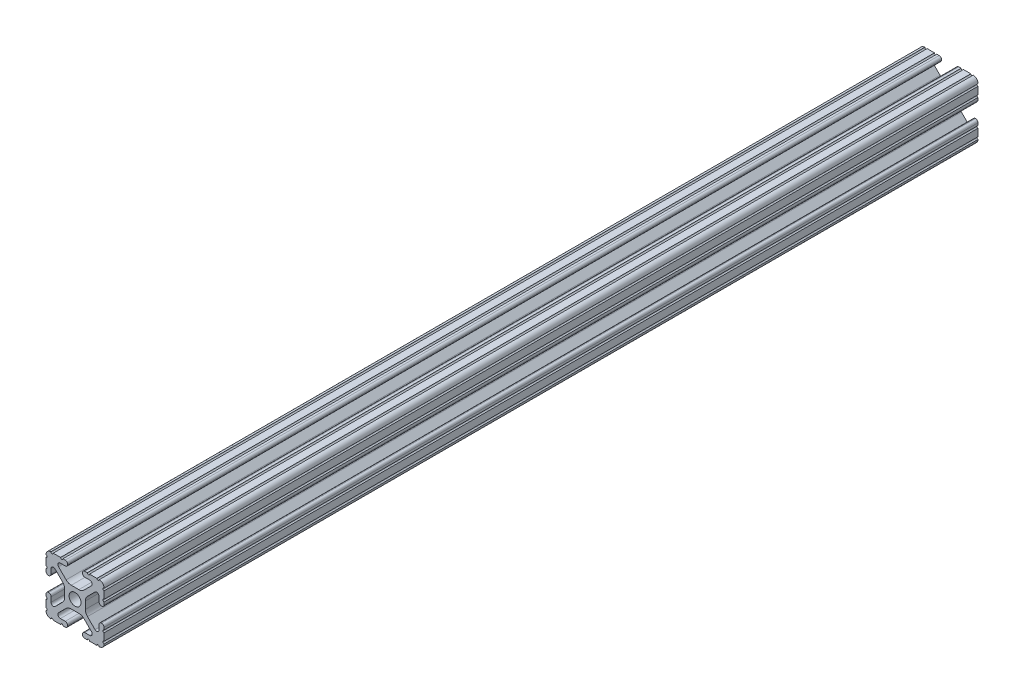
SolidWorks part; units mm, degrees
ref_plane "Front Plane" through (0, 0, 0) normal (0, 0, 1) x (1, 0, 0)
ref_plane "Top Plane" through (0, 0, 0) normal (0, 1, 0) x (1, 0, 0)
ref_plane "Right Plane" through (0, 0, 0) normal (1, 0, 0) x (0, 0, -1)
sketch "Sketch1" plane through (0, 0, 0) normal (0, 0, 1) x (1, 0, 0)
  line L88 (-7.1797, -8.6452) -> (-3.9523, -5.4237)
  line L89 (-1.7093, -4.4958) -> (1.7093, -4.4958)
  line L90 (3.9523, -5.4237) -> (7.1797, -8.6452)
  line L91 (6.4164, -10.4902) -> (4.2875, -10.4902)
  line L92 (3.2385, -11.5392) -> (3.2385, -11.651)
  line L93 (4.2875, -12.7) -> (5.3171, -12.7)
  line L94 (6.3331, -12.7) -> (9.5504, -12.7)
  line L95 (12.7, -9.5504) -> (12.7, -6.3331)
  line L96 (12.7, -5.3171) -> (12.7, -4.2875)
  line L97 (11.651, -3.2385) -> (11.5392, -3.2385)
  line L98 (10.4902, -4.2875) -> (10.4902, -6.4021)
  line L99 (8.7371, -7.1294) -> (5.441, -3.8408)
  line L100 (4.5085, -1.5932) -> (4.5085, 1.5932)
  line L101 (5.441, 3.8408) -> (8.7371, 7.1294)
  line L102 (10.4902, 6.4021) -> (10.4902, 4.2875)
  line L103 (11.5392, 3.2385) -> (11.651, 3.2385)
  line L104 (12.7, 4.2875) -> (12.7, 5.3171)
  line L105 (12.7, 6.3331) -> (12.7, 9.5504)
  line L106 (9.5504, 12.7) -> (6.3331, 12.7)
  line L107 (5.3171, 12.7) -> (4.2875, 12.7)
  line L108 (3.2385, 11.651) -> (3.2385, 11.5392)
  line L109 (4.2875, 10.4902) -> (6.4768, 10.4902)
  line L110 (7.207, 8.7244) -> (3.8983, 5.4232)
  line L111 (1.6558, 4.4958) -> (-1.6558, 4.4958)
  line L112 (-3.8983, 5.4232) -> (-7.207, 8.7244)
  line L113 (-6.4768, 10.4902) -> (-4.2875, 10.4902)
  line L114 (-3.2385, 11.5392) -> (-3.2385, 11.651)
  line L115 (-4.2875, 12.7) -> (-5.3171, 12.7)
  line L116 (-6.3331, 12.7) -> (-9.5504, 12.7)
  line L117 (-12.7, 9.5504) -> (-12.7, 6.3331)
  line L118 (-12.7, 5.3171) -> (-12.7, 4.2875)
  line L119 (-11.651, 3.2385) -> (-11.5392, 3.2385)
  line L120 (-10.4902, 4.2875) -> (-10.4902, 6.4021)
  line L121 (-8.7371, 7.1294) -> (-5.441, 3.8408)
  line L122 (-4.5085, 1.5932) -> (-4.5085, -1.5932)
  line L123 (-5.441, -3.8408) -> (-8.7371, -7.1294)
  line L124 (-10.4902, -6.4021) -> (-10.4902, -4.2875)
  line L125 (-11.5392, -3.2385) -> (-11.651, -3.2385)
  line L126 (-12.7, -4.2875) -> (-12.7, -5.3171)
  line L127 (-12.7, -6.3331) -> (-12.7, -9.5504)
  line L128 (-9.5504, -12.7) -> (-6.3331, -12.7)
  line L129 (-5.3171, -12.7) -> (-4.2875, -12.7)
  line L130 (-3.2385, -11.651) -> (-3.2385, -11.5392)
  line L131 (-4.2875, -10.4902) -> (-6.4164, -10.4902)
  circle A1 centre (0, 0) radius 2.6035
  arc A104 (-7.1797, -8.6452) -> (-6.4164, -10.4902) centre (-6.4164, -9.4098) ccw
  arc A105 (-1.7093, -4.4958) -> (-3.9523, -5.4237) centre (-1.7093, -7.6708) ccw
  arc A106 (3.9523, -5.4237) -> (1.7093, -4.4958) centre (1.7093, -7.6708) ccw
  arc A107 (6.4164, -10.4902) -> (7.1797, -8.6452) centre (6.4164, -9.4098) ccw
  arc A108 (4.2875, -10.4902) -> (3.2385, -11.5392) centre (4.2875, -11.5392) ccw
  arc A109 (3.2385, -11.651) -> (4.2875, -12.7) centre (4.2875, -11.651) ccw
  arc A110 (6.3331, -12.7) -> (5.3171, -12.7) centre (5.8251, -12.7) ccw
  arc A111 (10.5664, -12.6998) -> (9.5504, -12.7) centre (10.0584, -12.7) ccw
  arc A112 (10.5664, -12.6998) -> (12.6998, -10.5664) centre (10.5918, -10.5918) ccw
  arc A113 (12.7, -9.5504) -> (12.6998, -10.5664) centre (12.7, -10.0584) ccw
  arc A114 (12.7, -5.3171) -> (12.7, -6.3331) centre (12.7, -5.8251) ccw
  arc A115 (12.7, -4.2875) -> (11.651, -3.2385) centre (11.651, -4.2875) ccw
  arc A116 (11.5392, -3.2385) -> (10.4902, -4.2875) centre (11.5392, -4.2875) ccw
  arc A117 (8.7371, -7.1294) -> (10.4902, -6.4021) centre (9.4628, -6.4021) ccw
  arc A118 (4.5085, -1.5932) -> (5.441, -3.8408) centre (7.6835, -1.5932) ccw
  arc A119 (5.441, 3.8408) -> (4.5085, 1.5932) centre (7.6835, 1.5932) ccw
  arc A120 (10.4902, 6.4021) -> (8.7371, 7.1294) centre (9.4628, 6.4021) ccw
  arc A121 (10.4902, 4.2875) -> (11.5392, 3.2385) centre (11.5392, 4.2875) ccw
  arc A122 (11.651, 3.2385) -> (12.7, 4.2875) centre (11.651, 4.2875) ccw
  arc A123 (12.7, 6.3331) -> (12.7, 5.3171) centre (12.7, 5.8251) ccw
  arc A124 (12.6998, 10.5664) -> (12.7, 9.5504) centre (12.7, 10.0584) ccw
  arc A125 (12.6998, 10.5664) -> (10.5664, 12.6998) centre (10.5918, 10.5918) ccw
  arc A126 (9.5504, 12.7) -> (10.5664, 12.6998) centre (10.0584, 12.7) ccw
  arc A127 (5.3171, 12.7) -> (6.3331, 12.7) centre (5.8251, 12.7) ccw
  arc A128 (4.2875, 12.7) -> (3.2385, 11.651) centre (4.2875, 11.651) ccw
  arc A129 (3.2385, 11.5392) -> (4.2875, 10.4902) centre (4.2875, 11.5392) ccw
  arc A130 (7.207, 8.7244) -> (6.4768, 10.4902) centre (6.4768, 9.4563) ccw
  arc A131 (1.6558, 4.4958) -> (3.8983, 5.4232) centre (1.6558, 7.6708) ccw
  arc A132 (-3.8983, 5.4232) -> (-1.6558, 4.4958) centre (-1.6558, 7.6708) ccw
  arc A133 (-6.4768, 10.4902) -> (-7.207, 8.7244) centre (-6.4768, 9.4563) ccw
  arc A134 (-4.2875, 10.4902) -> (-3.2385, 11.5392) centre (-4.2875, 11.5392) ccw
  arc A135 (-3.2385, 11.651) -> (-4.2875, 12.7) centre (-4.2875, 11.651) ccw
  arc A136 (-6.3331, 12.7) -> (-5.3171, 12.7) centre (-5.8251, 12.7) ccw
  arc A137 (-10.5664, 12.6998) -> (-9.5504, 12.7) centre (-10.0584, 12.7) ccw
  arc A138 (-10.5664, 12.6998) -> (-12.6998, 10.5664) centre (-10.5918, 10.5918) ccw
  arc A139 (-12.7, 9.5504) -> (-12.6998, 10.5664) centre (-12.7, 10.0584) ccw
  arc A140 (-12.7, 5.3171) -> (-12.7, 6.3331) centre (-12.7, 5.8251) ccw
  arc A141 (-12.7, 4.2875) -> (-11.651, 3.2385) centre (-11.651, 4.2875) ccw
  arc A142 (-11.5392, 3.2385) -> (-10.4902, 4.2875) centre (-11.5392, 4.2875) ccw
  arc A143 (-8.7371, 7.1294) -> (-10.4902, 6.4021) centre (-9.4628, 6.4021) ccw
  arc A144 (-4.5085, 1.5932) -> (-5.441, 3.8408) centre (-7.6835, 1.5932) ccw
  arc A145 (-5.441, -3.8408) -> (-4.5085, -1.5932) centre (-7.6835, -1.5932) ccw
  arc A146 (-10.4902, -6.4021) -> (-8.7371, -7.1294) centre (-9.4628, -6.4021) ccw
  arc A147 (-10.4902, -4.2875) -> (-11.5392, -3.2385) centre (-11.5392, -4.2875) ccw
  arc A148 (-11.651, -3.2385) -> (-12.7, -4.2875) centre (-11.651, -4.2875) ccw
  arc A149 (-12.7, -6.3331) -> (-12.7, -5.3171) centre (-12.7, -5.8251) ccw
  arc A150 (-12.6998, -10.5664) -> (-12.7, -9.5504) centre (-12.7, -10.0584) ccw
  arc A151 (-12.6998, -10.5664) -> (-10.5664, -12.6998) centre (-10.5918, -10.5918) ccw
  arc A152 (-9.5504, -12.7) -> (-10.5664, -12.6998) centre (-10.0584, -12.7) ccw
  arc A153 (-5.3171, -12.7) -> (-6.3331, -12.7) centre (-5.8251, -12.7) ccw
  arc A154 (-4.2875, -12.7) -> (-3.2385, -11.651) centre (-4.2875, -11.651) ccw
  arc A155 (-3.2385, -11.5392) -> (-4.2875, -10.4902) centre (-4.2875, -11.5392) ccw
extrude "Boss-Extrude1" add sketch "Sketch1" along normal mid plane 609.6
sketch "Sketch2" plane through (0, 0, 304.8) normal (0, 0, 1) x (1, 0, 0)
  line L1 (-16.1874, 14.7999) -> (17.3899, 14.7999)
  line L2 (-16.1874, 14.7999) -> (-16.1874, -17.9449)
  line L3 (-16.1874, -17.9449) -> (17.3899, -17.9449)
  line L4 (17.3899, 14.7999) -> (17.3899, -17.9449)
extrude "Cut-Extrude1" cut sketch "Sketch2" against normal blind 227.33
